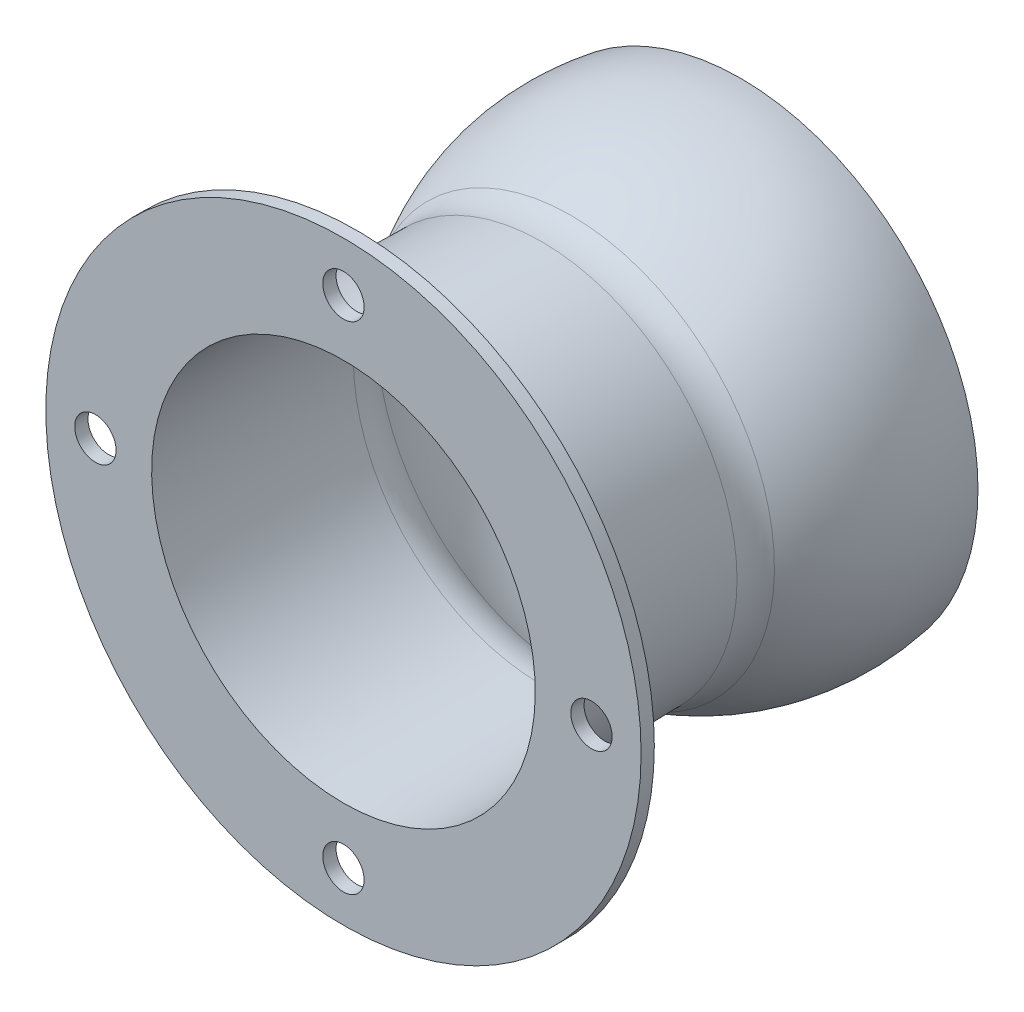
SolidWorks part; units mm, degrees
ref_plane "Front Plane" through (0, 0, 0) normal (0, 0, 1) x (1, 0, 0)
ref_plane "Top Plane" through (0, 0, 0) normal (0, 1, 0) x (1, 0, 0)
ref_plane "Right Plane" through (0, 0, 0) normal (1, 0, 0) x (0, 0, -1)
sketch "Sketch1" plane through (0, 0, 0) normal (1, 0, 0) x (0, 0, -1)
  line L0 (0, 0) -> (-50.9598, 0)
  line L2 (-50.9598, 34.2209) -> (-50.9598, 33.1794) construction
  line L6 (0, 35.8772) -> (0, 34.8622)
  line L7 (-24.752, 31.7091) -> (-24.752, 0) construction
  line L8 (0, 34.8622) -> (0, 0)
  line L9 (-50.9598, 33.1794) -> (-50.9598, 0) construction
  line L10 (-1.8421, 31.7091) -> (-37.0117, 31.7091) construction
  line L11 (-30.0543, 0) -> (-30.0543, 29.5)
  line L12 (-30.0543, 29.5) -> (-60.0543, 30)
  line L13 (22.9099, 34.8622) -> (-36.6675, 34.8622) construction
  line L14 (-24.752, 31.7091) -> (-24.752, 32.7091) construction
  line L15 (-6.1471, 0) -> (0, 34.8622) construction
  line L16 (-41.1471, 0) -> (-50.9598, 34.2209) construction
  line L19 (-60.0543, 0) -> (-50.9598, 0)
  line L20 (-60.0543, 30) -> (-60.0543, 0)
  line L21 (-41.1471, 0) -> (-28.9712, 33.4531) construction
  arc A0 (-28.9712, 33.4531) -> (-50.9598, 34.2209) centre (-41.1471, 0) ccw construction
  arc A1 (-19.6609, 32.7191) -> (0, 34.8622) centre (-6.1471, 0) cw construction
  arc A2 (-20.0427, 33.6433) -> (0, 35.8772) centre (-6.1471, 0) cw
  arc A3 (-28.9712, 33.4531) -> (-24.752, 32.7091) centre (-24.752, 45.0454) ccw construction
  arc A4 (-50.9598, 33.1794) -> (-29.3132, 32.5134) centre (-41.1471, 0) cw construction
  arc A5 (-29.3132, 32.5134) -> (-24.752, 31.7091) centre (-24.752, 45.0454) ccw construction
  arc A6 (-24.752, 32.7091) -> (-20.0427, 33.6433) centre (-24.752, 45.0454) ccw construction
  arc A7 (-24.752, 31.7091) -> (-19.6609, 32.7191) centre (-24.752, 45.0454) ccw construction
  arc A9 (-20.0427, 33.6433) -> (-25.6374, 30.7423) centre (-6.1471, 0) ccw
  arc A10 (-25.6374, 30.7423) -> (-30.0543, 29.5) centre (-29.9209, 37.4989) cw
  point P9 (0, 0)
  point P10 (-6.1471, 35.4)
revolve "Revolve1" add sketch "Sketch1" angle 360 about L0
shell "Shell1" thickness 1
sketch "Sketch2" plane through (0, 0, 60.0543) normal (0, 0, 1) x (1, 0, 0)
  line L0 (0, 0) -> (0, 37.5) construction
  circle A0 centre (0, 0) radius 45
  circle A1 centre (0, 37.5) radius 3.125
  circle A2 centre (37.5, 0) radius 3.125
  circle A3 centre (0, -37.5) radius 3.125
  circle A4 centre (-37.5, 0) radius 3.125
  circle A5 centre (0, 0) radius 28.9999 construction
  circle A6 centre (0, 0) radius 28.9999
  point P7 (0, 0)
  dimension "D1" = 90
  dimension "D2" = 6.25
  dimension "D5" = 37.5
  dimension "D4" = 4
extrude "Boss-Extrude1" add sketch "Sketch2" against normal blind 2
equation "\"Nominal_Diameter\"= 35mm"
equation "\"D1@Sketch1\"=\"Nominal_Diameter\" + 0.6mm"
equation "\"Wall_Thickness\"= 1mm"
equation "\"D5@Sketch1\"=\"Wall_Thickness\""
equation "\"D2@Sketch1\"=\"Nominal_Diameter\" + 0.4mm"
equation "\"D3@Sketch1\"=\"Nominal_Diameter\""
